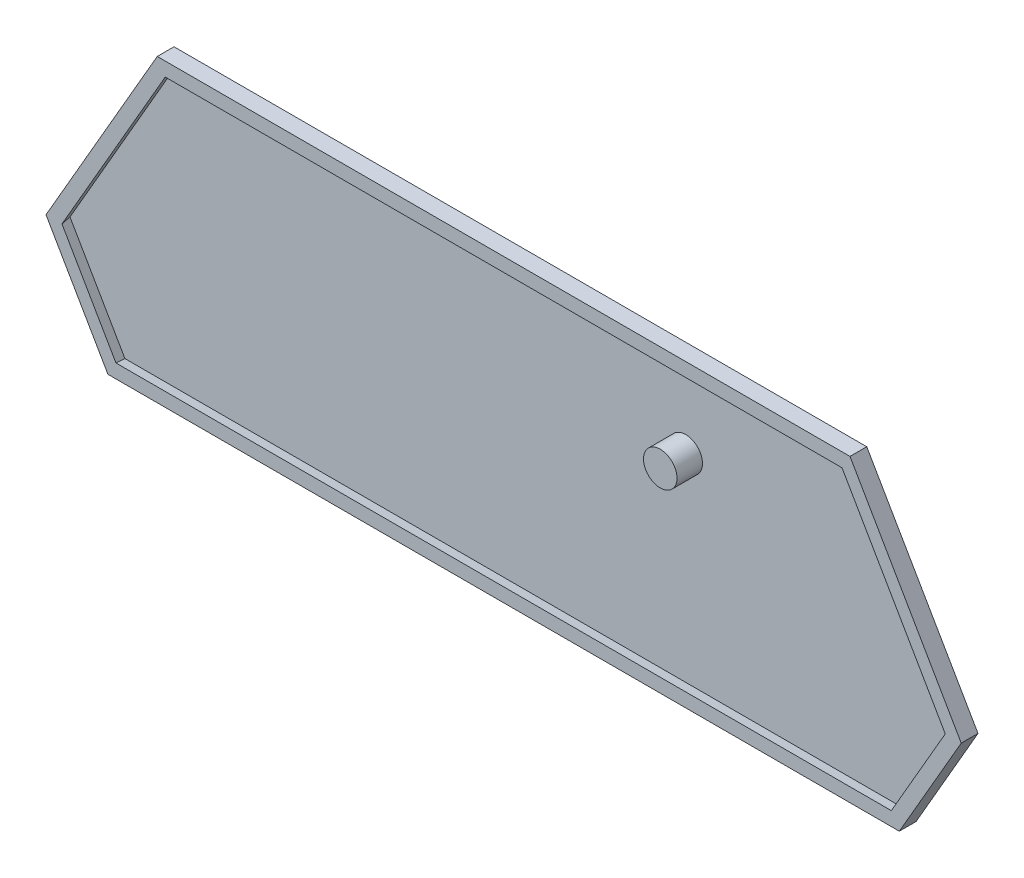
SolidWorks part; units mm, degrees
ref_plane "Plan de face" through (0, 0, 0) normal (0, 0, 1) x (1, 0, 0)
ref_plane "Plan de dessus" through (0, 0, 0) normal (0, 1, 0) x (1, 0, 0)
ref_plane "Plan de droite" through (0, 0, 0) normal (1, 0, 0) x (0, 0, -1)
sketch "Esquisse1" plane through (0, 0, 0) normal (0, 0, 1) x (1, 0, 0)
  line L30 (32.25, -42.5625) -> (2.7, -42.5625)
  line L31 (32.25, -44.0446) -> (32.25, -42.5625)
  line L32 (42.75, -44.0446) -> (32.25, -44.0446)
  line L33 (42.75, -42.5625) -> (42.75, -44.0446)
  line L34 (57.7649, -42.5625) -> (42.75, -42.5625)
  line L35 (65.7427, -28.7446) -> (57.7649, -42.5625)
  line L36 (50.4068, -2.1821) -> (65.7427, -28.7446)
  line L37 (-50.4068, -2.1821) -> (50.4068, -2.1821)
  line L38 (-65.7427, -28.7446) -> (-50.4068, -2.1821)
  line L39 (-57.7649, -42.5625) -> (-65.7427, -28.7446)
  line L40 (-42.75, -42.5625) -> (-57.7649, -42.5625)
  line L41 (-42.75, -44.0446) -> (-42.75, -42.5625)
  line L42 (-32.25, -44.0446) -> (-42.75, -44.0446)
  line L43 (-32.25, -42.5625) -> (-32.25, -44.0446)
  line L44 (-2.7, -42.5625) -> (-32.25, -42.5625)
  line L45 (-2.7, -44.7446) -> (-2.7, -42.5625)
  line L46 (-59.0248, -44.7446) -> (-2.7, -44.7446)
  line L47 (-68.2624, -28.7446) -> (-59.0248, -44.7446)
  line L48 (-51.6667, 0) -> (-68.2624, -28.7446)
  line L49 (51.6667, 0) -> (-51.6667, 0)
  line L50 (68.2624, -28.7446) -> (51.6667, 0)
  line L51 (59.0248, -44.7446) -> (68.2624, -28.7446)
  line L52 (2.7, -44.7446) -> (59.0248, -44.7446)
  line L53 (2.7, -42.5625) -> (2.7, -44.7446)
  line L70 (-59.0248, -44.7446) -> (2.7, -44.7446)
  line L71 (-68.2624, -28.7446) -> (-59.0248, -44.7446)
  line L72 (-51.6667, 0) -> (-68.2624, -28.7446)
  line L73 (51.6667, 0) -> (-51.6667, 0)
  line L74 (68.2624, -28.7446) -> (51.6667, 0)
  line L75 (59.0248, -44.7446) -> (68.2624, -28.7446)
  line L76 (2.7, -44.7446) -> (59.0248, -44.7446)
  dimension "D1" = 0
extrude "Boss.-Extru.1" add sketch "Esquisse1" along normal blind 1
sketch "Esquisse2" plane through (0, 0, 1) normal (0, 0, 1) x (1, 0, 0)
  line L6 (-68.2624, -28.7446) -> (-59.0248, -44.7446)
  line L7 (-59.0248, -44.7446) -> (59.0248, -44.7446)
  line L8 (59.0248, -44.7446) -> (68.2624, -28.7446)
  line L9 (68.2624, -28.7446) -> (51.6667, 0)
  line L10 (51.6667, 0) -> (-51.6667, 0)
  line L11 (-51.6667, 0) -> (-68.2624, -28.7446)
  line L12 (-68.2624, -28.7446) -> (-59.0248, -44.7446)
  line L13 (-59.0248, -44.7446) -> (59.0248, -44.7446)
  line L14 (59.0248, -44.7446) -> (68.2624, -28.7446)
  line L15 (68.2624, -28.7446) -> (51.6667, 0)
  line L16 (51.6667, 0) -> (-51.6667, 0)
  line L17 (-51.6667, 0) -> (-68.2624, -28.7446)
  dimension "D1" = 0
extrude "Extru.-Mince1" add sketch "Esquisse2" along normal blind 1.5 draft 10 thin thin type one direction reverse wall 1.8 draft outward yes
sketch "Esquisse3" plane through (0, 0, 0) normal (0, 0, -1) x (-1, 0, 0)
  line L6 (59.0248, -44.7446) -> (68.2624, -28.7446)
  line L7 (68.2624, -28.7446) -> (51.6667, 0)
  line L8 (51.6667, 0) -> (-51.6667, 0)
  line L9 (-51.6667, 0) -> (-68.2624, -28.7446)
  line L10 (-68.2624, -28.7446) -> (-59.0248, -44.7446)
  line L11 (-59.0248, -44.7446) -> (59.0248, -44.7446)
  line L12 (59.0248, -44.7446) -> (68.2624, -28.7446)
  line L13 (68.2624, -28.7446) -> (51.6667, 0)
  line L14 (51.6667, 0) -> (-51.6667, 0)
  line L15 (-51.6667, 0) -> (-68.2624, -28.7446)
  line L16 (-68.2624, -28.7446) -> (-59.0248, -44.7446)
  line L17 (-59.0248, -44.7446) -> (59.0248, -44.7446)
  dimension "D1" = 0
extrude "Enlèv. de mat.-Extru.-Mince1" cut sketch "Esquisse3" against normal through all thin
sketch "Esquisse4" plane through (0, 0, 1) normal (0, 0, 1) x (1, 0, 0)
  circle A0 centre (25.6655, -13.4245) radius 2.5
  dimension "D1" = 5
extrude "Boss.-Extru.2" add sketch "Esquisse4" along normal blind 3.8
sketch "Esquisse5" plane through (0, 0, 1) normal (0, 0, 1) x (1, 0, 0)
  line L0 (-18.3, -12.3) -> (-18.3, -16.3)
  line L1 (-18.3, -16.3) -> (-28.5, -16.3)
  line L2 (-28.5, -16.3) -> (-28.5, -12.3)
extrude "Extru.-Mince2" [suppressed] add sketch "Esquisse5" along normal blind 4.5 thin
fillet "Congé1" [suppressed] radius 1
